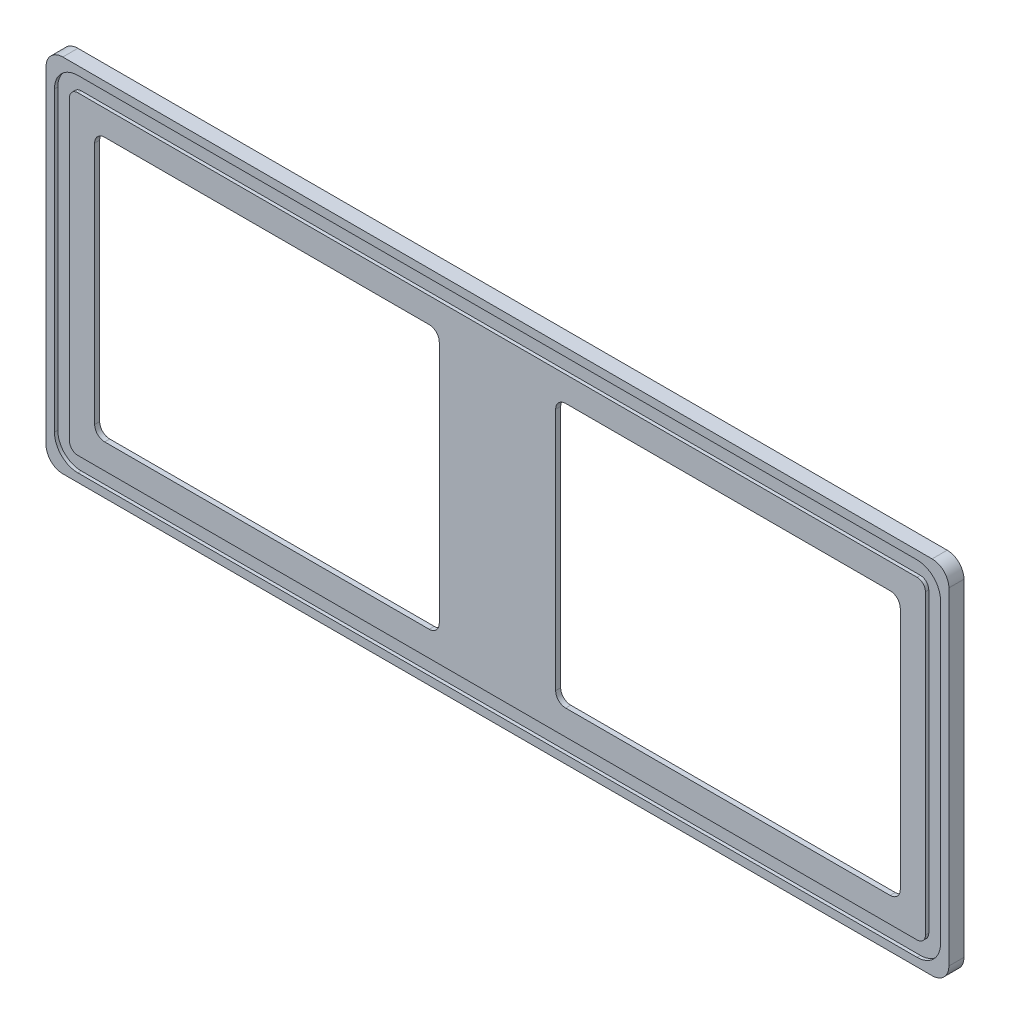
SolidWorks part; units mm, degrees
ref_plane "Front Plane" through (0, 0, 0) normal (0, 0, 1) x (1, 0, 0)
ref_plane "Top Plane" through (0, 0, 0) normal (0, 1, 0) x (1, 0, 0)
ref_plane "Right Plane" through (0, 0, 0) normal (1, 0, 0) x (0, 0, -1)
sketch "Sketch1" plane through (0, 0, 0) normal (0, 0, 1) x (1, 0, 0)
  line L1 (259.35, -9) -> (-259.35, -9)
  line L2 (269.35, 1) -> (269.35, 196.4)
  line L3 (259.35, 206.4) -> (-259.35, 206.4)
  line L4 (-269.35, 1) -> (-269.35, 196.4)
  arc A0 (269.35, 196.4) -> (259.35, 206.4) centre (259.35, 196.4) ccw
  arc A1 (259.35, -9) -> (269.35, 1) centre (259.35, 1) ccw
  arc A2 (-259.35, -9) -> (-269.35, 1) centre (-259.35, 1) cw
  arc A3 (-259.35, 206.4) -> (-269.35, 196.4) centre (-259.35, 196.4) ccw
  dimension "D1" = 10
extrude "Boss-Extrude1" add sketch "Sketch1" along normal blind 9
sketch "Sketch4" plane through (0, 0, 9) normal (0, 0, 1) x (1, 0, 0)
  line L4 (-269.35, 196.4) -> (-269.35, 1) construction
  line L5 (-250.35, -4) -> (250.35, -4)
  line L6 (-264.35, 10) -> (-264.35, 187.4)
  line L7 (-250.35, 201.4) -> (250.35, 201.4)
  line L8 (264.35, 10) -> (264.35, 187.4)
  line L9 (259.35, 206.4) -> (-259.35, 206.4) construction
  line L10 (269.35, 1) -> (269.35, 196.4) construction
  line L11 (-259.35, -9) -> (259.35, -9) construction
  line L12 (-250.35, 5) -> (250.35, 5)
  line L13 (255.35, 10) -> (255.35, 187.4)
  line L14 (-250.35, 192.4) -> (250.35, 192.4)
  line L15 (-255.35, 10) -> (-255.35, 187.4)
  line L16 (-264.35, 201.4) -> (264.35, 201.4) construction
  line L17 (264.35, -4) -> (264.35, 201.4) construction
  line L18 (-264.35, -4) -> (264.35, -4) construction
  line L19 (-264.35, -4) -> (-264.35, 201.4) construction
  line L20 (255.35, 5) -> (255.35, 192.4) construction
  line L21 (-255.35, 192.4) -> (255.35, 192.4) construction
  line L22 (-255.35, 5) -> (255.35, 5) construction
  line L23 (-255.35, 5) -> (-255.35, 192.4) construction
  arc A4 (250.35, 201.4) -> (264.35, 187.4) centre (250.35, 187.4) cw
  arc A5 (250.35, -4) -> (264.35, 10) centre (250.35, 10) ccw
  arc A6 (-250.35, -4) -> (-264.35, 10) centre (-250.35, 10) cw
  arc A7 (-264.35, 187.4) -> (-250.35, 201.4) centre (-250.35, 187.4) cw
  arc A8 (255.35, 187.4) -> (250.35, 192.4) centre (250.35, 187.4) ccw
  arc A9 (250.35, 5) -> (255.35, 10) centre (250.35, 10) ccw
  arc A10 (-250.35, 5) -> (-255.35, 10) centre (-250.35, 10) cw
  arc A11 (-250.35, 192.4) -> (-255.35, 187.4) centre (-250.35, 187.4) ccw
  dimension "D6" = 14
  dimension "D7" = 5
  dimension "D1" = 5
  dimension "D2" = 5
  dimension "D3" = 5
  dimension "D4" = 5
  dimension "D5" = 9
extrude "Cut-Extrude1" cut sketch "Sketch4" against normal blind 2
sketch "Sketch5" plane through (0, 0, 0) normal (0, 0, 1) x (1, 0, 0)
  line L0 (-255.35, 187.4) -> (-255.35, 10) construction
  line L1 (-234.35, 177.4) -> (-40.7313, 177.4)
  line L2 (-240.35, 171.4) -> (-240.35, 26)
  line L3 (-234.35, 20) -> (-40.7313, 20)
  line L4 (-34.7313, 171.4) -> (-34.7313, 26)
  line L5 (250.35, 192.4) -> (-250.35, 192.4) construction
  line L6 (-250.35, 5) -> (250.35, 5) construction
  arc A0 (-240.35, 26) -> (-234.35, 20) centre (-234.35, 26) ccw
  arc A1 (-40.7313, 20) -> (-34.7313, 26) centre (-40.7313, 26) ccw
  arc A2 (-40.7313, 177.4) -> (-34.7313, 171.4) centre (-40.7313, 171.4) cw
  arc A3 (-234.35, 177.4) -> (-240.35, 171.4) centre (-234.35, 171.4) ccw
  dimension "D4" = 6
  dimension "D1" = 15
  dimension "D2" = 15
  dimension "D3" = 15
extrude "Cut-Extrude2" cut sketch "Sketch5" along normal up to surface (9 mm away) up to face at (0, 98.7, 9)
sketch "Sketch7" plane through (0, 0, 0) normal (0, 0, -1) x (-1, 0, 0)
  line L8 (250.35, 26) -> (250.35, 171.4)
  line L9 (40.7313, 10) -> (234.35, 10)
  line L10 (24.7313, 171.4) -> (24.7313, 26)
  line L11 (234.35, 187.4) -> (40.7313, 187.4)
  line L12 (250.35, 26) -> (250.35, 171.4)
  line L13 (40.7313, 10) -> (234.35, 10)
  line L14 (24.7313, 171.4) -> (24.7313, 26)
  line L15 (234.35, 187.4) -> (40.7313, 187.4)
  arc A8 (234.35, 10) -> (250.35, 26) centre (234.35, 26) ccw
  arc A9 (24.7313, 26) -> (40.7313, 10) centre (40.7313, 26) ccw
  arc A10 (40.7313, 187.4) -> (24.7313, 171.4) centre (40.7313, 171.4) ccw
  arc A11 (250.35, 171.4) -> (234.35, 187.4) centre (234.35, 171.4) ccw
  arc A12 (234.35, 10) -> (250.35, 26) centre (234.35, 26) ccw
  arc A13 (24.7313, 26) -> (40.7313, 10) centre (40.7313, 26) ccw
  arc A14 (40.7313, 187.4) -> (24.7313, 171.4) centre (40.7313, 171.4) ccw
  arc A15 (250.35, 171.4) -> (234.35, 187.4) centre (234.35, 171.4) ccw
  dimension "D1" = 10
extrude "Cut-Extrude4" cut sketch "Sketch7" against normal blind 6
mirror "Mirror1" about plane through (0, 0, 0) normal (1, 0, 0) of "Cut-Extrude4", "Cut-Extrude2"
